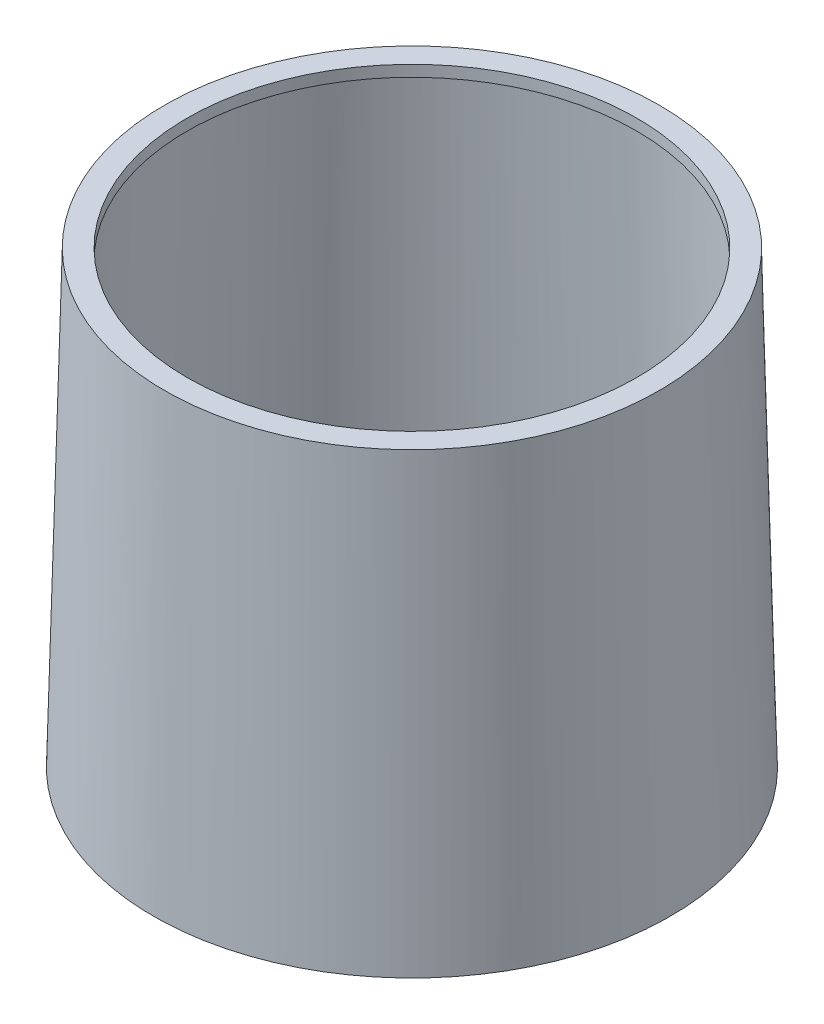
SolidWorks part; units mm, degrees
ref_plane "Front Plane" through (0, 0, 0) normal (0, 0, 1) x (1, 0, 0)
ref_plane "Top Plane" through (0, 0, 0) normal (0, 1, 0) x (1, 0, 0)
ref_plane "Right Plane" through (0, 0, 0) normal (1, 0, 0) x (0, 0, -1)
sketch "Sketch3" plane through (0, 0, 0) normal (0, 0, 1) x (1, 0, 0)
  line L0 (0, 0) -> (11.5, 0)
  line L1 (0, 0) -> (0, 20)
  line L2 (0, 20) -> (11, 20)
  line L3 (11, 20) -> (11.5, 0)
  dimension "0.6" = 11
  dimension "D2" = 11.5
  dimension "D3" = 20
revolve "Revolve1" add sketch "Sketch3" angle 360 about L1
sketch "Sketch6" plane through (0, 20, 0) normal (0, 1, 0) x (1, 0, 0)
  circle A0 centre (0, 0) radius 10
  circle A1 centre (0, 0) radius 11 construction
  dimension "D1" = 1
extrude "Cut-Extrude1" cut sketch "Sketch6" against normal blind 20
sketch "Sketch7" plane through (0, 0, 0) normal (0, 0, 1) x (1, 0, 0)
  line L7 (10, 19.5) -> (10, 0.5)
  line L8 (0, 0) -> (0, 24.971) construction
  line L12 (10, 0) -> (10, 20) construction
  line L14 (11.25, 0.5) -> (10.6076, 19.5)
  line L15 (10.6076, 19.5) -> (10, 19.5)
  line L16 (11.25, 0.5) -> (10, 0.5)
  line L17 (11, 20) -> (-11, 20) construction
  line L18 (-11.5, 0) -> (11.5, 0) construction
  dimension "D1" = 0.5
  dimension "D2" = 0.5
revolve "Cut-Revolve1" cut sketch "Sketch7" angle 360 about L8
sketch "Sketch8" plane through (0, 0, 0) normal (0, -1, 0) x (-1, 0, 0)
  circle A0 centre (0, 0) radius 10.5
  circle A1 centre (0, 0) radius 11
  circle A2 centre (0, 0) radius 11.5 construction
  circle A3 centre (0, 0) radius 10 construction
  dimension "D1" = 0.5
  dimension "D2" = 0.5
extrude "Cut-Extrude3" cut sketch "Sketch8" against normal blind 0.5
